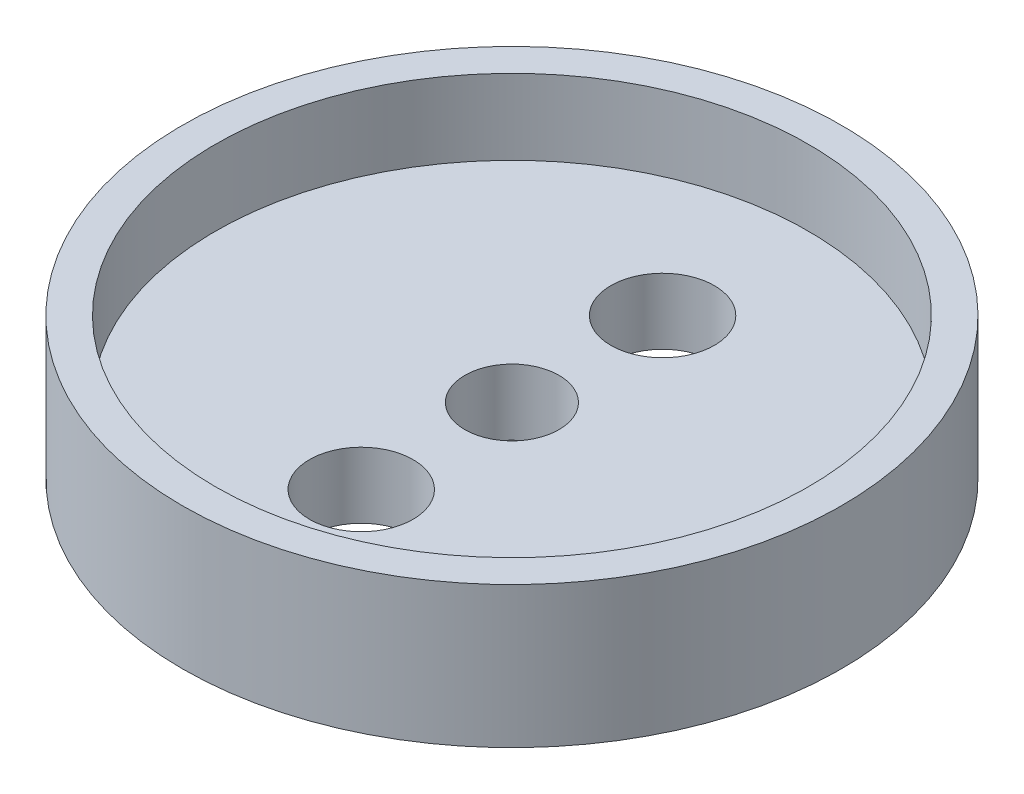
SolidWorks part; units mm, degrees
ref_plane "Front Plane" through (0, 0, 0) normal (0, 0, 1) x (1, 0, 0)
ref_plane "Top Plane" through (0, 0, 0) normal (0, 1, 0) x (1, 0, 0)
ref_plane "Right Plane" through (0, 0, 0) normal (1, 0, 0) x (0, 0, -1)
sketch "Sketch4" plane through (0, 0, 0) normal (0, 1, 0) x (1, 0, 0)
  line L0 (0, 2.5) -> (0, 8) construction
  line L1 (0, -2.5) -> (0, -8) construction
  circle A1 centre (0, 0) radius 17.5
  circle A4 centre (0, -8) radius 2.75
  circle A5 centre (0, 8) radius 2.75
  circle A6 centre (0, 0) radius 2.5 construction
  circle A7 centre (0, 0) radius 2.5
  dimension "D1" = 5
  dimension "D2" = 35
  dimension "D4" = 5.5
  dimension "D3" = 5.5
extrude "LidBase" add sketch "Sketch4" along normal blind 7.5
sketch "Sketch5" plane through (0, 7.5, 0) normal (0, 1, 0) x (1, 0, 0)
  circle A1 centre (0, 0) radius 15.75
  dimension "D1" = 31.5
extrude "LidGrooves" cut sketch "Sketch5" against normal blind 4
